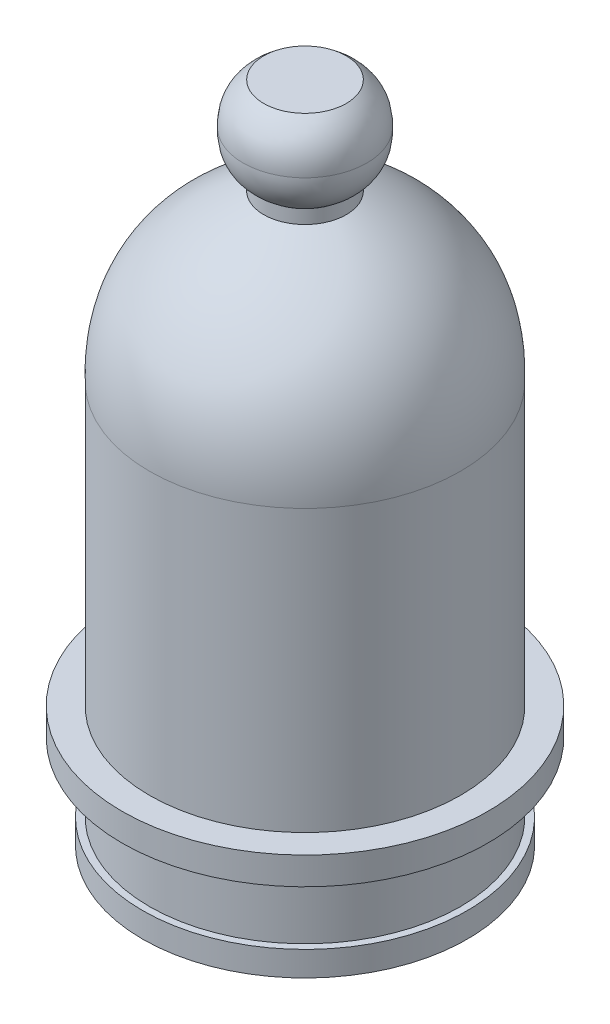
SolidWorks part; units mm, degrees
ref_plane "Front Plane" through (0, 0, 0) normal (0, 0, 1) x (1, 0, 0)
ref_plane "Top Plane" through (0, 0, 0) normal (0, 1, 0) x (1, 0, 0)
ref_plane "Right Plane" through (0, 0, 0) normal (1, 0, 0) x (0, 0, -1)
sketch "Sketch1" plane through (0, 0, 0) normal (0, 1, 0) x (1, 0, 0)
  circle A0 centre (0, 0) radius 11.8
  dimension "D1" = 23.6
extrude "Boss-Extrude1" add sketch "Sketch1" along normal blind 1.8
sketch "Sketch2" plane through (0, 1.8, 0) normal (0, 1, 0) x (1, 0, 0)
  circle A0 centre (0, 0) radius 11.3
  dimension "D1" = 22.6
extrude "Boss-Extrude2" add sketch "Sketch2" along normal blind 5 contours A0
sketch "Sketch3" plane through (0, 6.8, 0) normal (0, 1, 0) x (1, 0, 0)
  circle A0 centre (0, 0) radius 13.3
  dimension "D1" = 26.6
extrude "Boss-Extrude3" add sketch "Sketch3" along normal blind 2
sketch "Sketch4" plane through (0, 8.8, 0) normal (0, 1, 0) x (1, 0, 0)
  circle A0 centre (0, 0) radius 11.3
  dimension "D1" = 22.6
extrude "Boss-Extrude4" add sketch "Sketch4" along normal blind 20.4 contours A0
sketch "Sketch5" plane through (0, 0, 0) normal (1, 0, 0) x (0, 0, -1)
  line L0 (-11.3, 29.2) -> (0, 29.2)
  line L1 (0, 29.2) -> (0, 41.2)
  line L2 (0, 41.2) -> (-3, 41.2)
  line L3 (0, 34.2) -> (-10.5, 34.2)
  spline S0 degree 2 poles (-11.3, 29.2) (-11.5405, 37.5377) (-3, 41.2) knots 0 0 0 1 1 1
  dimension "D5" = 11.3
  dimension "D1" = 12
  dimension "D2" = 3
  dimension "D3" = 5
  dimension "D4" = 10.5
revolve "Revolve1" add sketch "Sketch5" angle 360 about L1
sketch "Sketch6" plane through (0, 41.2, 0) normal (0, 1, 0) x (1, 0, 0)
  circle A0 centre (0, 0) radius 3
  circle A1 centre (0, 0) radius 3 construction
extrude "Boss-Extrude5" add sketch "Sketch6" along normal blind 1
sketch "Sketch7" plane through (0, 0, 0) normal (1, 0, 0) x (0, 0, -1)
  line L0 (0, 42.2) -> (0, 45.2)
  line L1 (3, 42.2) -> (-3, 42.2) construction
  line L2 (0, 45.2) -> (-4.5, 45.2)
  line L3 (0, 43.7) -> (-4.25, 43.7)
  line L4 (-3, 42.2) -> (0, 42.2)
  spline S0 degree 2 poles (-3, 42.2) (-4.5763, 43.3211) (-4.5, 45.2) knots 0 0 0 1 1 1
  dimension "D1" = 3
  dimension "D2" = 4.5
  dimension "D3" = 4.25
revolve "Revolve2" add sketch "Sketch7" angle 360 about L0
mirror "Mirror1" about plane through (0, 45.2, 0) normal (0, -1, 0) of "Revolve2"
